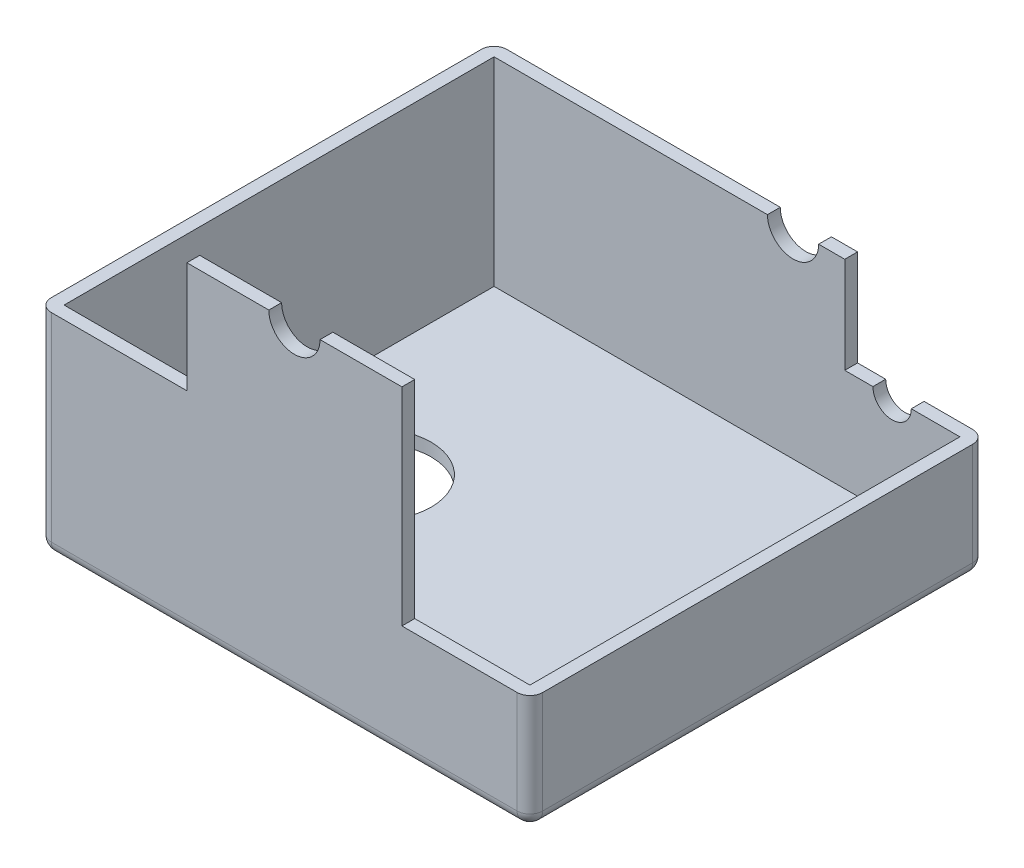
SolidWorks part; units mm, degrees
ref_plane "Front" through (0, 0, 0) normal (0, 0, 1) x (1, 0, 0)
ref_plane "Top" through (0, 0, 0) normal (0, 1, 0) x (1, 0, 0)
ref_plane "Right" through (0, 0, 0) normal (1, 0, 0) x (0, 0, -1)
sketch "Sketch1" plane through (0, 0, 0) normal (0, 1, 0) x (1, 0, 0)
  line L1 (0, 0) -> (96, 0)
  line L2 (0, 0) -> (0, -89)
  line L3 (0, -89) -> (96, -89)
  line L4 (96, 0) -> (96, -89)
  dimension "D1" = 96
  dimension "D2" = 89
extrude "Boss-Extrude1" add sketch "Sketch1" along normal blind 72.5
sketch "Sketch3" plane through (0, 72.5, 0) normal (0, 1, 0) x (1, 0, 0)
  line L8 (2.5, -2.5) -> (2.5, -86.5)
  line L9 (2.5, -86.5) -> (93.5, -86.5)
  line L10 (93.5, -86.5) -> (93.5, -2.5)
  line L11 (93.5, -2.5) -> (2.5, -2.5)
  line L12 (2.5, -2.5) -> (2.5, -86.5)
  line L13 (2.5, -86.5) -> (93.5, -86.5)
  line L14 (93.5, -86.5) -> (93.5, -2.5)
  line L15 (93.5, -2.5) -> (2.5, -2.5)
  dimension "D1" = 2.5
extrude "Cut-Extrude1" cut sketch "Sketch3" against normal blind 70 contours L12 L13 L14 L15
sketch "Sketch4" plane through (0, 0, 0) normal (0, -1, 0) x (1, 0, 0)
  line L2 (0, 0) -> (0, 89) construction
  line L3 (0, 89) -> (96, 89) construction
  circle A0 centre (22.7, 46) radius 11
  dimension "D1" = 22
  dimension "D2" = 22.7
  dimension "D3" = 43
extrude "Cut-Extrude3" cut sketch "Sketch4" against normal blind 10
sketch "Sketch6" plane through (0, 0, 0) normal (0, 0, -1) x (-1, 0, 0)
  line L1 (-96, 72.5) -> (-96, 0) construction
  line L2 (-96, 22.55) -> (-71, 22.55)
  line L3 (-71, 22.55) -> (-71, 41.34)
  line L4 (-71, 41.34) -> (0, 41.34)
  line L5 (0, 72.5) -> (0, 0) construction
  line L6 (0, 41.34) -> (0, 72.5)
  line L7 (0, 72.5) -> (-96, 72.5)
  line L8 (-96, 72.5) -> (-96, 22.55)
  line L9 (-96, 0) -> (0, 0) construction
  point P16 (-71, 31.945)
  dimension "D1" = 22.55
  dimension "D2" = 31.16
  dimension "D3" = 25
extrude "Cut-Extrude4" cut sketch "Sketch6" against normal through all
sketch "Sketch7" plane through (0, 0, 0) normal (0, 0, -1) x (-1, 0, 0)
  line L0 (-96, 22.55) -> (-71, 22.55) construction
  line L1 (-71, 41.34) -> (0, 41.34) construction
  line L2 (-96, 22.55) -> (-96, 0) construction
  line L3 (-84, 22.55) -> (-76.5, 22.55)
  line L4 (-65.9, 41.34) -> (-55.9, 41.34)
  arc A0 (-84, 22.55) -> (-76.5, 22.55) centre (-80.25, 22.55) ccw
  arc A1 (-65.9, 41.34) -> (-55.9, 41.34) centre (-60.9, 41.34) ccw
  dimension "D3" = 5
  dimension "D4" = 3.75
  dimension "D1" = 15.75
  dimension "D2" = 35.1
extrude "Cut-Extrude5" cut sketch "Sketch7" against normal blind 10
sketch "Sketch8" plane through (0, 0, 89) normal (0, 0, 1) x (1, 0, 0)
  line L0 (29, 41.34) -> (29, 63)
  line L1 (71, 41.34) -> (0, 41.34) construction
  line L2 (29, 63) -> (71, 63)
  line L3 (71, 63) -> (71, 41.34)
  line L4 (71, 41.34) -> (29, 41.34)
  line L5 (71, 22.55) -> (71, 41.34) construction
  dimension "D1" = 0
  dimension "D2" = 42
  dimension "D3" = 21.66
extrude "Boss-Extrude2" add sketch "Sketch8" against normal blind 2.5
sketch "Sketch9" plane through (0, 0, 89) normal (0, 0, 1) x (1, 0, 0)
  line L0 (71, 63) -> (29, 63) construction
  line L1 (96, 22.55) -> (96, 0) construction
  line L2 (45, 63) -> (55, 63)
  arc A0 (45, 63) -> (55, 63) centre (50, 63) ccw
  dimension "D1" = 5
  dimension "D2" = 46
extrude "Cut-Extrude6" cut sketch "Sketch9" against normal blind 2.5
fillet "Fillet1" radius 2.5 8 edges at (0, 20.67, 0) (96, 0, 44.5) (48, 0, 0) (96, 11.275, 0) (96, 11.275, 89) (48, 0, 89) (0, 0, 44.5) (0, 20.67, 89)
